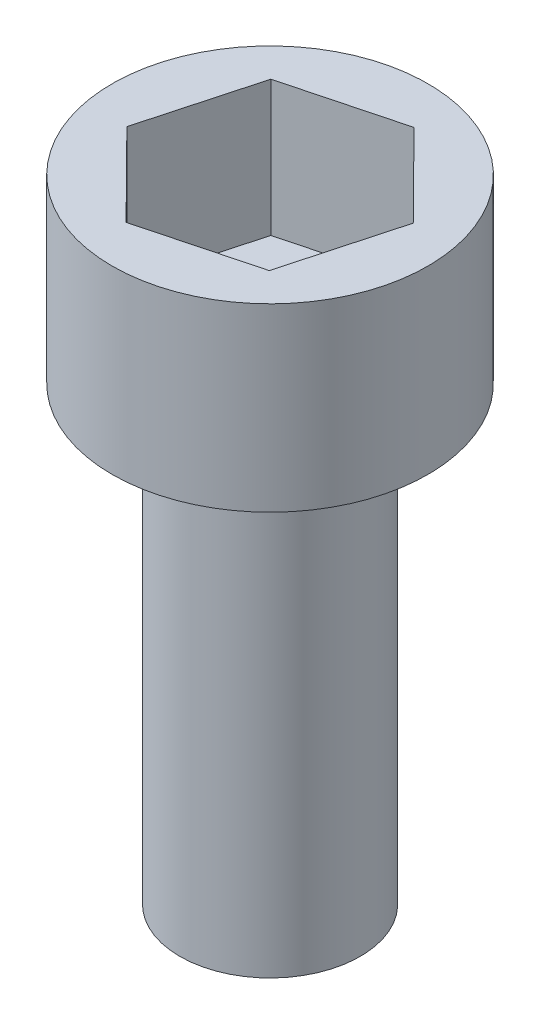
SolidWorks part; units mm, degrees
ref_plane "Front Plane" through (0, 0, 0) normal (0, 0, 1) x (1, 0, 0)
ref_plane "Top Plane" through (0, 0, 0) normal (0, 1, 0) x (1, 0, 0)
ref_plane "Right Plane" through (0, 0, 0) normal (1, 0, 0) x (0, 0, -1)
sketch "Sketch1" plane through (0, 0, 0) normal (0, 1, 0) x (1, 0, 0)
  circle A0 centre (0, 0) radius 2
extrude "Boss-Extrude1" add sketch "Sketch1" along normal blind 10
sketch "Sketch2" plane through (0, 10, 0) normal (0, 1, 0) x (1, 0, 0)
  circle A0 centre (0, 0) radius 3.5
extrude "Boss-Extrude2" add sketch "Sketch2" along normal blind 4
sketch "Sketch3" plane through (0, 14, 0) normal (0, 1, 0) x (1, 0, 0)
  line L1 (2.5127, 0.6606) -> (0.6842, 2.5064)
  line L2 (0.6842, 2.5064) -> (-1.8285, 1.8457)
  line L3 (-1.8285, 1.8457) -> (-2.5127, -0.6606)
  line L4 (-2.5127, -0.6606) -> (-0.6842, -2.5064)
  line L5 (-0.6842, -2.5064) -> (1.8285, -1.8457)
  line L6 (1.8285, -1.8457) -> (2.5127, 0.6606)
  circle A0 centre (0, 0) radius 2.25 construction
extrude "Cut-Extrude1" cut sketch "Sketch3" against normal blind 3
